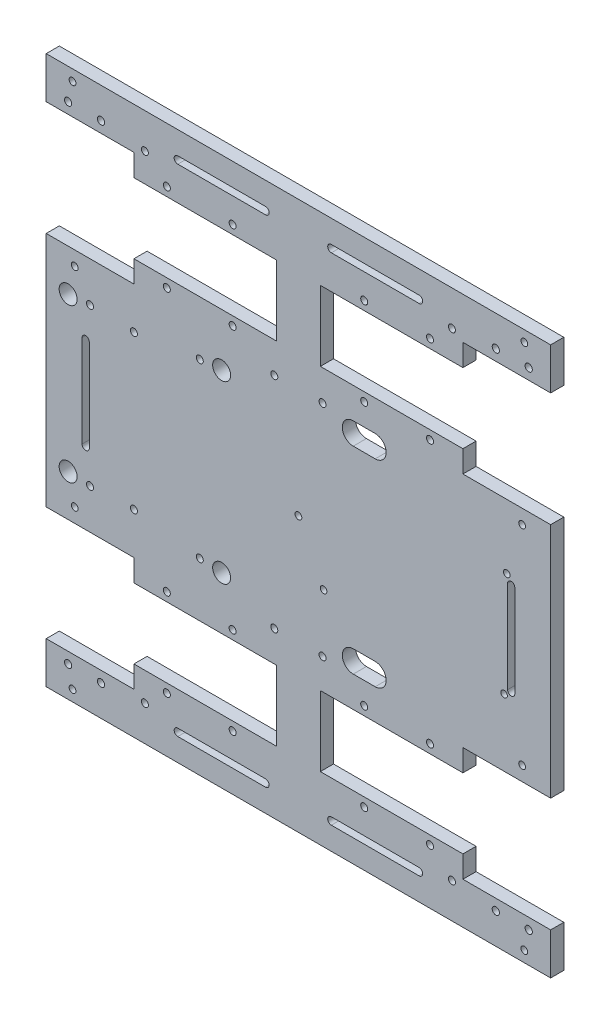
SolidWorks part; units mm, degrees
material "Balsa"
ref_plane "Plano frontal" through (0, 0, 0) normal (0, 0, 1) x (1, 0, 0)
ref_plane "Plano superior" through (0, 0, 0) normal (0, 1, 0) x (1, 0, 0)
ref_plane "Plano direito" through (0, 0, 0) normal (1, 0, 0) x (0, 0, -1)
sketch "Esboço1" plane through (0, 0, 0) normal (0, 0, 1) x (1, 0, 0)
  line L1 (-115, 125) -> (115, 125)
  line L2 (-115, 125) -> (-115, -125)
  line L3 (-115, -125) -> (115, -125)
  line L4 (115, 125) -> (115, -125)
  line L5 (-115, 125) -> (115, -125) construction
  line L6 (-115, -125) -> (115, 125) construction
  point P0 (0, 0)
  dimension "D1" = 250
  dimension "D2" = 230
extrude "Ressalto-extrusão1" add sketch "Esboço1" along normal blind 6
sketch "Esboço2" plane through (0, 0, 6) normal (0, 0, 1) x (1, 0, 0)
  line L0 (-75, 64) -> (-75, 54)
  line L1 (-115, 106) -> (-75, 106)
  line L2 (-115, 106) -> (-115, 54)
  line L3 (-115, 54) -> (-75, 54)
  line L4 (-75, 106) -> (-75, 96)
  line L5 (-94.2985, 0) -> (0, 0) construction
  line L6 (0, 0) -> (0, 90.2057) construction
  line L8 (-115, 125) -> (-115, -125) construction
  line L9 (-75, 96) -> (-10, 96)
  line L10 (-10, 80) -> (-79.3144, 80) construction
  line L11 (-75, 64) -> (-10, 64)
  line L12 (-10, 96) -> (-10, 64)
  line L13 (115, 125) -> (-115, 125) construction
  circle A0 centre (-60, 100) radius 1.6
  circle A1 centre (-30, 100) radius 1.6
  circle A2 centre (-30, 60) radius 1.6
  circle A3 centre (-60, 60) radius 1.6
  point P4 (-10, 80)
  point P17 (-115, 80)
  dimension "D7" = 3.2
  dimension "D2" = 45
  dimension "D3" = 0
  dimension "D4" = 52
  dimension "D5" = 65
  dimension "D6" = 32
  dimension "D8" = 15
  dimension "D9" = 30
  dimension "D10" = 40
  dimension "D11" = 105
extrude "motor" cut sketch "Esboço2" against normal blind 6
sketch "Esboço4" plane through (0, 0, 6) normal (0, 0, 1) x (1, 0, 0)
  line L0 (-105, 0) -> (-35, 0) construction
  line L1 (-115, 125) -> (-115, 106) construction
  line L2 (-105, 35) -> (-35, 40) construction
  circle A0 centre (-105, 35) radius 4.1
  circle A1 centre (-44.9746, 39.2875) radius 1.6
  circle A2 centre (-95.0254, 35.7125) radius 1.6
  circle A3 centre (-35, 40) radius 4.1
  circle A4 centre (-44.9746, -39.2875) radius 1.6
  circle A5 centre (-35, -40) radius 4.1
  circle A6 centre (-95.0254, -35.7125) radius 1.6
  circle A7 centre (-105, -35) radius 4.1
  circle A8 centre (-75, 35) radius 1.6
  circle A9 centre (-75, -35) radius 1.6
  dimension "D1" = 8.2
  dimension "D4" = 3.2
  dimension "D6" = 8.2
  dimension "D2" = 70
  dimension "D5" = 70
  dimension "D7" = 80
  dimension "D8" = 10
  dimension "D3" = 10
  dimension "D9" = 10
  dimension "D10" = 30
extrude "garra" cut sketch "Esboço4" against normal blind 10
sketch "Esboço7" plane through (0, 0, 6) normal (0, 0, 1) x (1, 0, 0)
  line L0 (-15, 113) -> (-55, 113) construction
  line L1 (-15, 111.35) -> (-55, 111.35)
  line L2 (-15, 114.65) -> (-55, 114.65)
  line L5 (0, 0) -> (0, 75.6274) construction
  line L6 (0, 0) -> (47.7764, 0) construction
  line L7 (115, 125) -> (-115, 125) construction
  line L8 (-115, 125) -> (-115, 106) construction
  arc A0 (-15, 111.35) -> (-15, 114.65) centre (-15, 113) ccw
  arc A1 (-55, 114.65) -> (-55, 111.35) centre (-55, 113) ccw
  circle A2 centre (-105, 111) radius 1.65
  circle A3 centre (-90, 111) radius 1.65
  point P2 (-35, 113)
  dimension "D1" = 12
  dimension "D2" = 1.65
  dimension "D7" = 3.3
  dimension "D3" = 40
  dimension "D4" = 15
  dimension "D5" = 10
  dimension "D6" = 14
  dimension "D8" = 15
extrude "sensores frontais" cut sketch "Esboço7" against normal blind 10
sketch "Esboço5" plane through (0, 0, 0) normal (0, 0, -1) x (-1, 0, 0)
  line L0 (0, -60.5357) -> (0, 0) construction
  line L1 (0, 0) -> (56.6107, 0) construction
  line L2 (-115, -125) -> (-115, 125) construction
  line L3 (-115, 125) -> (115, 125) construction
  line L4 (-115, -125) -> (-115, 125) construction
  line L6 (-115, 125) -> (115, 125) construction
  circle A0 centre (70, 109) radius 1.6
  circle A3 centre (-102, 47.5) radius 1.55
  circle A4 centre (-103, 120) radius 1.55
  circle A5 centre (11, 50) radius 1.6
  circle A9 centre (0, 0) radius 1.55
  circle A10 centre (-11, 50) radius 1.6
  circle A11 centre (-11, -50) radius 1.6
  circle A12 centre (11, -50) radius 1.6
  dimension "D3" = 3.1
  dimension "D6" = 3.1
  dimension "D7" = 100
  dimension "D8" = 3.2
  dimension "D11" = 3.2
  dimension "D1" = 47.5
  dimension "D2" = 13
  dimension "D4" = 5
  dimension "D5" = 12
  dimension "D9" = 11
  dimension "D10" = 16
  dimension "D12" = 70
extrude "maos francesas" cut sketch "Esboço5" against normal blind 10
mirror "Espelhar1" about plane through (0, 0, 0) normal (1, 0, 0) of "maos francesas", "motor", "sensores frontais"
mirror "Espelhar2" about plane through (0, 0, 0) normal (0, 1, 0) of "motor", "Espelhar1", "sensores frontais", "maos francesas"
sketch "Esboço6" plane through (0, 0, 6) normal (0, 0, 1) x (1, 0, 0)
  line L0 (-87, -20) -> (-87, 20) construction
  line L1 (-88.65, -20) -> (-88.65, 20)
  line L2 (-85.35, -20) -> (-85.35, 20)
  line L3 (-100, -20) -> (-100, 20) construction
  line L4 (-101.65, -20) -> (-101.65, 20)
  line L5 (-98.35, -20) -> (-98.35, 20)
  line L6 (-115, 54) -> (-115, -54) construction
  arc A0 (-88.65, -20) -> (-85.35, -20) centre (-87, -20) ccw
  arc A1 (-85.35, 20) -> (-88.65, 20) centre (-87, 20) ccw
  arc A2 (-101.65, -20) -> (-98.35, -20) centre (-100, -20) ccw
  arc A3 (-98.35, 20) -> (-101.65, 20) centre (-100, 20) ccw
  point P2 (-87, 0)
  point P8 (-100, 0)
  dimension "D2" = 1.65
  dimension "D1" = 40
  dimension "D3" = 13
  dimension "D4" = 15
extrude "Corte-extrusão2" [suppressed] cut sketch "Esboço6" against normal blind 10
sketch "Esboço8" plane through (0, 0, 6) normal (0, 0, 1) x (1, 0, 0)
  line L0 (-97, -21) -> (-97, 21) construction
  line L1 (-98.65, -21) -> (-98.65, 21)
  line L2 (-95.35, -21) -> (-95.35, 21)
  line L3 (-115, 54) -> (-115, -54) construction
  line L4 (0, 0) -> (0, 43.5193) construction
  line L5 (97, -21) -> (97, 21) construction
  line L6 (98.65, -21) -> (98.65, 21)
  line L7 (95.35, -21) -> (95.35, 21)
  arc A0 (-98.65, -21) -> (-95.35, -21) centre (-97, -21) ccw
  arc A1 (-95.35, 21) -> (-98.65, 21) centre (-97, 21) ccw
  arc A2 (98.65, -21) -> (95.35, -21) centre (97, -21) cw
  arc A3 (95.35, 21) -> (98.65, 21) centre (97, 21) cw
  point P2 (-97, 0)
  point P14 (97, 0)
  dimension "D1" = 1.65
  dimension "D2" = 42
  dimension "D3" = 18
extrude "Sensores laterais" cut sketch "Esboço8" against normal blind 10
sketch "Esboço9" plane through (0, 0, 0) normal (0, 0, -1) x (-1, 0, 0)
  line L0 (-35, 45) -> (-25, 45) construction
  line L1 (-35, 50) -> (-25, 50)
  line L2 (-35, 40) -> (-25, 40)
  line L3 (0, 0) -> (-121.4816, 0) construction
  line L4 (-35, -45) -> (-25, -45) construction
  line L5 (-35, -50) -> (-25, -50)
  line L6 (-35, -40) -> (-25, -40)
  arc A0 (-35, 50) -> (-35, 40) centre (-35, 45) ccw
  arc A1 (-25, 40) -> (-25, 50) centre (-25, 45) ccw
  arc A2 (-35, -50) -> (-35, -40) centre (-35, -45) cw
  arc A3 (-25, -40) -> (-25, -50) centre (-25, -45) cw
  point P2 (-30, 45)
  point P12 (-30, -45)
  dimension "D2" = 5
  dimension "D1" = 10
  dimension "D3" = 45
  dimension "D4" = 25
extrude "Fios" cut sketch "Esboço9" against normal blind 10
sketch "Esboço10" plane through (0, 0, 0) normal (0, 0, -1) x (-1, 0, 0)
  line L0 (-115, -54) -> (-115, 54) construction
  circle A0 centre (-95, 24.6867) radius 1.5
  circle A1 centre (-93.76, -23.4833) radius 1.5
  circle A2 centre (-11.46, -23.4833) radius 1.5
  dimension "D1" = 3
  dimension "D2" = 82.3
  dimension "D3" = 48.17
  dimension "D4" = 1.24
  dimension "D5" = 20
extrude "Corte-extrusão7" cut sketch "Esboço10" against normal blind 10
equation "\"D9@Esboço4\"=\"D3@Esboço4\""
